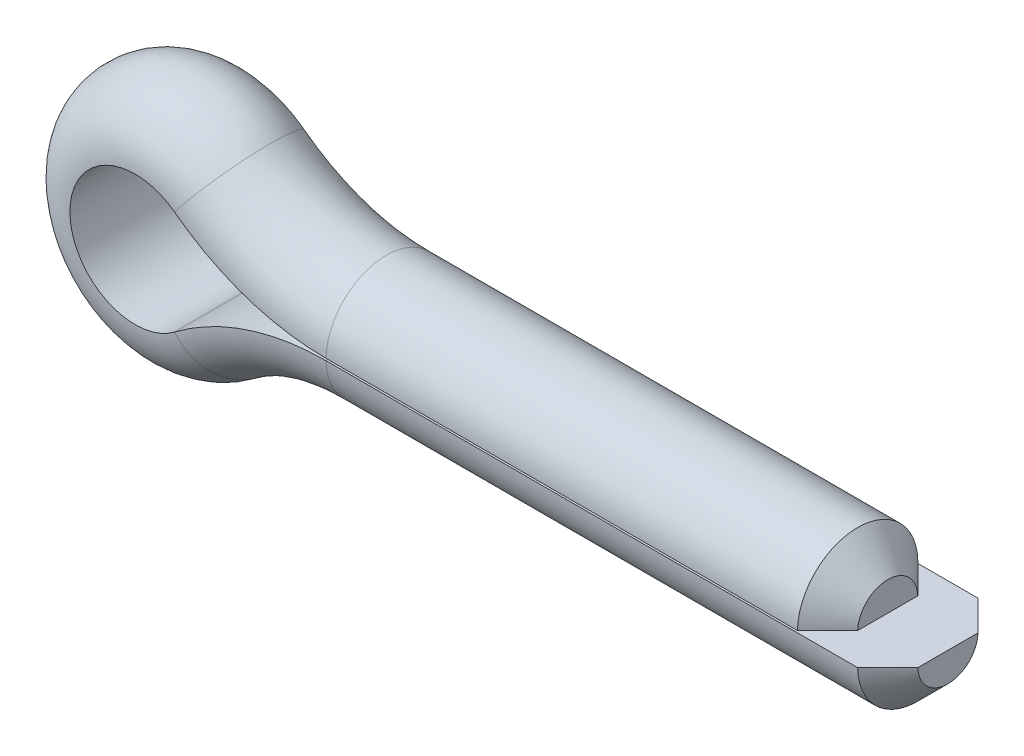
SolidWorks part; units mm, degrees
material "1060 Alloy"
ref_plane "Front" through (0, 0, 0) normal (0, 0, 1) x (1, 0, 0)
ref_plane "Top" through (0, 0, 0) normal (0, 1, 0) x (1, 0, 0)
ref_plane "Right" through (0, 0, 0) normal (1, 0, 0) x (0, 0, -1)
sketch "Sketch1" plane through (0, 0, 0) normal (0, 0, 1) x (1, 0, 0)
  line L0 (-17.5343, 0) -> (1.524, 0) construction
  line L1 (-12.7, -0.0254) -> (1.524, -0.0254)
  line L2 (-15.8835, 0.0254) -> (1.524, 0.0254) construction
  line L3 (-12.7, 0.0254) -> (0, 0.0254)
  line L4 (-11.4985, 0.0254) -> (1.524, 0.0254) construction
  line L5 (-11.4985, -0.0254) -> (1.524, -0.0254) construction
  line L6 (-17.5343, 1.5875) -> (-17.5343, 0) construction
  line L7 (-17.5343, 1.5875) -> (-17.5343, 3.175) construction
  line L8 (-11.4985, 0) -> (1.524, 0) construction
  line L9 (0, 0.0254) -> (0, 0) construction
  line L10 (-17.5343, 0) -> (-17.5343, -3.175) construction
  line L11 (-12.7, 1.4986) -> (-12.7, -1.5494) construction
  arc A1 (-16.5367, 1.3156) -> (-16.5367, -1.3156) centre (-17.5343, 0) ccw
  arc A2 (-12.7, -0.0254) -> (-16.5367, -1.3156) centre (-12.7, -6.3754) ccw
  arc A3 (-16.5367, 1.3156) -> (-12.7, 0.0254) centre (-12.7, 6.3754) ccw
  circle A4 centre (-17.5343, 0) radius 3.175 construction
  point P15 (0, 0.0254)
  dimension "D6" = 6.35
  dimension "Head Diameter" = 6.35
  dimension "ExtendedProngLength" = 1.524
  dimension "Length" = 12.7
  dimension "Diameter" = 3.048
  dimension "D1" = 1.524
  dimension "D4" = 0.0254
  dimension "D5" = 0.0254
sketch "Sketch2" plane through (0, 0, 0) normal (1, 0, 0) x (0, 0, -1)
  line L0 (-1.5238, 0.0254) -> (1.5238, 0.0254)
  line L1 (0, 1.524) -> (0, -1.524) construction
  circle A1 centre (0, 0) radius 1.524 construction
  arc A2 (-1.5238, 0.0254) -> (1.5238, 0.0254) centre (0, 0) cw
  point P5 (0, 0)
  dimension "D1" = 1.524
sketch "Sketch3" plane through (0, 0, 0) normal (0, 0, 1) x (1, 0, 0)
  line L0 (-12.7, -0.0254) -> (1.524, -0.0254) construction
  line L1 (-12.7, 0.0254) -> (0, 0.0254) construction
  line L2 (-12.7, -0.0254) -> (1.524, -0.0254)
  line L3 (-12.7, 0.0254) -> (0, 0.0254)
  arc A0 (-12.7, -0.0254) -> (-16.5367, -1.3156) centre (-12.7, -6.3754) ccw construction
  arc A1 (-16.5367, 1.3156) -> (-12.7, 0.0254) centre (-12.7, 6.3754) ccw construction
  arc A2 (-16.5367, 1.3156) -> (-16.5367, -1.3156) centre (-17.5343, 0) ccw construction
  arc A3 (-12.7, -0.0254) -> (-16.5367, -1.3156) centre (-12.7, -6.3754) ccw
  arc A4 (-16.5367, 1.3156) -> (-12.7, 0.0254) centre (-12.7, 6.3754) ccw
  arc A5 (-16.5367, 1.3156) -> (-16.5367, -1.3156) centre (-17.5343, 0) ccw
sketch "Sketch4" plane through (0, 0, 0) normal (1, 0, 0) x (0, 0, -1)
  line L0 (-1.5238, 0.0254) -> (1.5238, 0.0254) construction
  line L1 (-1.5238, 0.0254) -> (1.5238, 0.0254)
  arc A2 (1.5238, 0.0254) -> (-1.5238, 0.0254) centre (0, 0) ccw construction
  arc A3 (1.5238, 0.0254) -> (-1.5238, 0.0254) centre (0, 0) ccw
sweep "Sweep1" add profiles "Sketch4" path "Sketch3"
chamfer "Chamfer1" distance 0.762 angle 45 2 edges at (1.524, -1.524, 0) (0, 1.524, 0)
equation "\"D6@Sketch1\"=\"Head Diameter@Sketch1\""
equation "\"D1@Sketch2\"=\"Diameter@Sketch1\"/2"
equation "\"ExtendedProngLength@Sketch1\" = \"Length@Sketch1\"*.09"
equation "\"D1@Chamfer1\"=\"Diameter@Sketch1\"/4"
equation "\"D1@Sketch1\"=\"Diameter@Sketch1\"/2"
